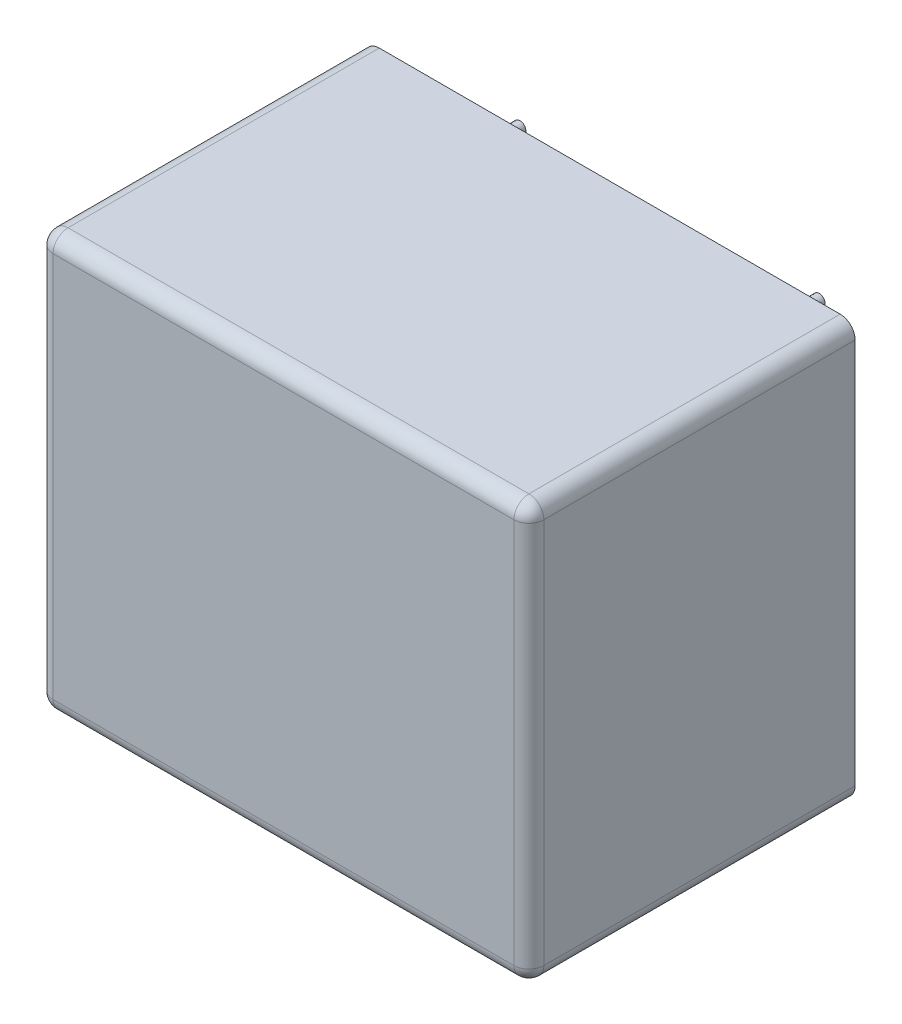
SolidWorks part; units mm, degrees
ref_plane "Přední rovina" through (0, 0, 0) normal (0, 0, 1) x (1, 0, 0)
ref_plane "Horní rovina" through (0, 0, 0) normal (0, 1, 0) x (1, 0, 0)
ref_plane "Pravá rovina" through (0, 0, 0) normal (1, 0, 0) x (0, 0, -1)
sketch "Skica1" plane through (0, 0, 0) normal (0, 0, 1) x (1, 0, 0)
  line L1 (1, 0) -> (31.8, 0)
  line L2 (0, 1) -> (0, 26.8)
  line L3 (1, 27.8) -> (31.8, 27.8)
  line L4 (32.8, 1) -> (32.8, 26.8)
  arc A0 (31.8, 0) -> (32.8, 1) centre (31.8, 1) ccw
  arc A1 (1, 0) -> (0, 1) centre (1, 1) cw
  arc A2 (0, 26.8) -> (1, 27.8) centre (1, 26.8) cw
  arc A3 (31.8, 27.8) -> (32.8, 26.8) centre (31.8, 26.8) cw
  point P7 (32.8, 0)
  point P10 (0, 0)
  point P13 (0, 27.8)
  dimension "D3" = 1
  dimension "D1" = 32.8
  dimension "D2" = 27.8
extrude "Přidat vysunutím1" add sketch "Skica1" along normal blind 21.8
fillet "Zaoblit1" radius 1 8 edges at (32.5071, 27.5071, 21.8) (32.8, 13.9, 21.8) (32.5071, 0.2929, 21.8) (16.4, 0, 21.8) (0.2929, 0.2929, 21.8) (0, 13.9, 21.8) (0.2929, 27.5071, 21.8) (16.4, 27.8, 21.8)
sketch "Skica2" plane through (0, 0, 0) normal (0, 0, 1) x (1, 0, 0)
  line L0 (0, 26.8) -> (0, 1) construction
  line L1 (1, 0) -> (31.8, 0) construction
  circle A0 centre (21.4, 3.9) radius 0.4
  circle A1 centre (26.4, 23.9) radius 0.4
  circle A2 centre (6.4, 23.9) radius 0.4
  circle A3 centre (11.4, 3.9) radius 0.4
  point P8 (0, 0)
  point P9 (0, 0)
  point P12 (0, 13.9)
  point P15 (16.4, 0)
  dimension "D1" = 0.8
  dimension "D2" = 0.8
  dimension "D3" = 0.8
  dimension "D4" = 0.8
  dimension "D5" = 20
  dimension "D6" = 10
  dimension "D7" = 20
  dimension "D8" = 10
  dimension "D9" = 5
  dimension "D10" = 10
extrude "Přidat vysunutím2" add sketch "Skica2" against normal blind 4
